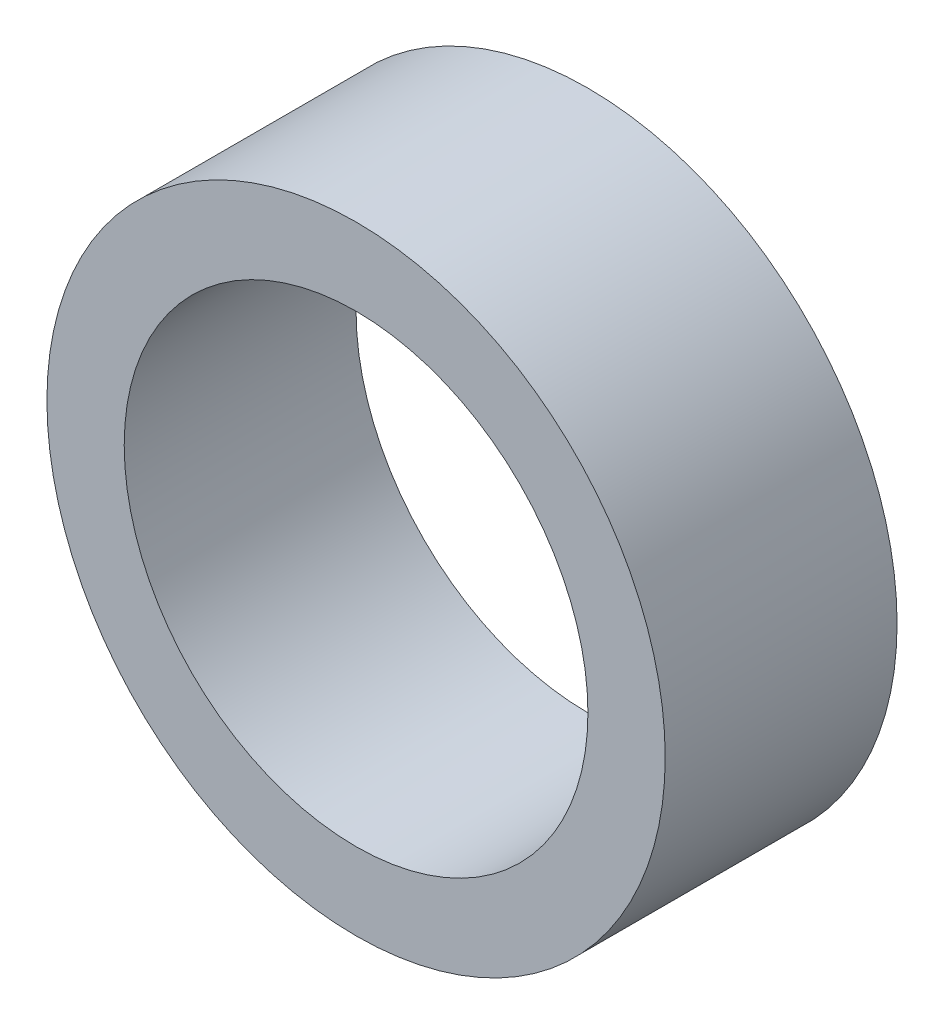
SolidWorks part; units mm, degrees
material "PTFE (general)"
ref_plane "Front Plane" through (0, 0, 0) normal (0, 0, 1) x (1, 0, 0)
ref_plane "Top Plane" through (0, 0, 0) normal (0, 1, 0) x (1, 0, 0)
ref_plane "Right Plane" through (0, 0, 0) normal (1, 0, 0) x (0, 0, -1)
sketch "Sketch1" plane through (0, 0, 0) normal (0, 0, 1) x (1, 0, 0)
  line L0 (-12.7, 0) -> (12.7, 0) construction
  line L1 (-9.525, 0) -> (9.525, 0) construction
  point P4 (0, 0)
  point P7 (0, 0)
  dimension "OD" = 25.4
  dimension "ID" = 19.05
  dimension "Wall Thickness" = 3.175
sketch "Sketch2" plane through (0, 0, 0) normal (1, 0, 0) x (0, 0, -1)
  line L0 (4.7625, 0) -> (-4.7625, 0) construction
  point P0 (33.3375, 0)
  point P4 (0, 0)
  point P6 (-33.3375, 0)
  dimension "D1" = 9.525
  dimension "D2" = 38.1
  dimension "D3" = 38.1
sketch "Sketch3" plane through (0, 0, 0) normal (0, 0, 1) x (1, 0, 0)
  circle A0 centre (0, 0) radius 12.7
  circle A1 centre (0, 0) radius 9.525
  dimension "D1" = 25.4
extrude "Boss-Extrude1" add sketch "Sketch3" along normal mid plane 9.525
equation "\"D2@Sketch2\"=\"OD@Sketch1\" * 1.5"
equation "\"D3@Sketch2\"=\"D2@Sketch2\""
equation "\"D1@Sketch3\" = \"OD@Sketch1\""
equation "\"D1@Boss-Extrude1\"=\"D1@Sketch2\""
